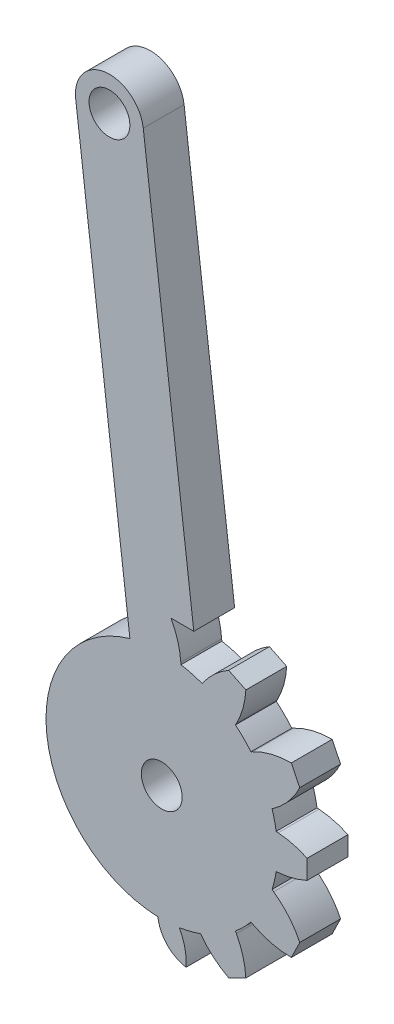
SolidWorks part; units mm, degrees
ref_plane "Front Plane" through (0, 0, 0) normal (0, 0, 1) x (1, 0, 0)
ref_plane "Top Plane" through (0, 0, 0) normal (0, 1, 0) x (1, 0, 0)
ref_plane "Right Plane" through (0, 0, 0) normal (1, 0, 0) x (0, 0, -1)
ref_plane "Plane1" through (0, 0, 1.9) normal (0, 0, 1) x (1, 0, 0)
sketch "Sketch1" plane through (0, 0, 1.9) normal (0, 0, 1) x (1, 0, 0)
  line L0 (-6.3198, 40.5143) -> (-2.3366, 8.1725)
  line L2 (0, 0) -> (-0.5241, -8.4838) construction
  line L3 (4.9124, -9.7818) -> (6.1789, -9.162)
  line L4 (5.4841, -6.684) -> (5.4141, -6.5527)
  line L5 (6.5527, -5.4141) -> (6.684, -5.4841)
  line L6 (9.5182, -6.1887) -> (10.138, -4.9222)
  line L7 (8.224, -2.6542) -> (8.1029, -2.5677)
  line L8 (8.4039, -1.2742) -> (8.5524, -1.2634)
  line L9 (10.6789, -0.705) -> (10.6789, 0.705)
  line L10 (8.5524, 1.2634) -> (8.4039, 1.2742)
  line L11 (8.1029, 2.5677) -> (8.224, 2.6542)
  line L12 (10.138, 4.9222) -> (9.5182, 6.1887)
  line L13 (6.684, 5.4841) -> (6.5527, 5.4141)
  line L14 (5.4141, 6.5527) -> (5.4841, 6.684)
  line L15 (6.1789, 9.162) -> (4.9124, 9.7818)
  line L16 (3.0542, 8.0862) -> (2.9677, 7.9651)
  line L17 (1.4124, 8.3818) -> (1.4016, 8.5302)
  line L18 (0.6785, 10.98) -> (2.3554, 10.98)
  line L19 (2.3554, 10.98) -> (-1.3573, 41.1255)
  line L20 (3.9551, -7.5277) -> (3.5177, -7.7418) construction
  line L21 (3.7364, -7.6347) -> (0, 0) construction
  circle A0 centre (-3.8386, 40.8199) radius 1.5
  arc A1 (-0.2838, -8.4953) -> (1.7876, -10.6761) centre (2.2, -8.2104) ccw
  arc A2 (6.1789, -9.162) -> (5.4841, -6.684) centre (0.1887, -9.5051) ccw
  arc A3 (5.4141, -6.5527) -> (6.5527, -5.4141) centre (0, 0) ccw
  arc A4 (6.684, -5.4841) -> (9.5182, -6.1887) centre (9.5051, -0.1887) ccw
  arc A5 (10.138, -4.9222) -> (8.224, -2.6542) centre (4.7381, -7.5377) ccw
  arc A6 (8.1029, -2.5677) -> (8.4039, -1.2742) centre (0, 0) ccw
  arc A7 (8.5524, -1.2634) -> (10.6789, -0.705) centre (8.1175, 4.7208) ccw
  arc A8 (10.6789, 0.705) -> (8.5524, 1.2634) centre (8.1175, -4.7208) ccw
  arc A9 (8.4039, 1.2742) -> (8.1029, 2.5677) centre (0, 0) ccw
  arc A10 (8.224, 2.6542) -> (10.138, 4.9222) centre (4.7381, 7.5377) ccw
  arc A11 (9.5182, 6.1887) -> (6.684, 5.4841) centre (9.5051, 0.1887) ccw
  arc A12 (6.5527, 5.4141) -> (5.4141, 6.5527) centre (0, 0) ccw
  arc A13 (5.4841, 6.684) -> (6.1789, 9.162) centre (0.1887, 9.5051) ccw
  arc A14 (4.9124, 9.7818) -> (3.0542, 8.0862) centre (7.9377, 4.6003) ccw
  arc A15 (2.9677, 7.9651) -> (1.4124, 8.3818) centre (0, 0) ccw
  arc A16 (1.4016, 8.5302) -> (0.6785, 10.98) centre (-4.5826, 8.0954) ccw
  arc A17 (-1.3573, 41.1255) -> (-6.3198, 40.5143) centre (-3.8386, 40.8199) ccw
  circle A18 centre (0, 0) radius 1.5
  circle A19 centre (0, 0) radius 8.5 construction
  arc A20 (2.8505, -8.0078) -> (4.9124, -9.7818) centre (7.6929, -4.465) ccw
  arc A21 (1.2894, -8.4016) -> (2.8505, -8.0078) centre (0, 0) ccw
  arc A22 (1.2894, -8.4016) -> (1.7876, -10.6761) centre (-2.2386, -10.3661) cw
  arc A23 (-0.2838, -8.4953) -> (-2.3366, 8.1725) centre (0, 0) cw
  point P61 (0, 0)
  point P62 (0, 0)
  point P64 (-0.2838, -8.4016)
  point P65 (0, 0)
  point P66 (0, 0)
  point P67 (0, 0)
  point P69 (0, 0)
  point P70 (0, 0)
  point P71 (0, 0)
  dimension "D1" = 3
  dimension "D2" = 2.5
  dimension "D3" = 1.61
  dimension "D4" = 8.5
  dimension "D5" = 6
  dimension "D6" = 0.6785
  dimension "D7" = 1.4016
  dimension "D8" = 1.4124
  dimension "D9" = 2.2
  dimension "D11" = 2.9677
  dimension "D12" = 3.0542
  dimension "D13" = 4.7381
  dimension "D14" = 4.9124
  dimension "D15" = 2.72
  dimension "D16" = 5.4141
  dimension "D17" = 6.5527
  dimension "D18" = 8.1175
  dimension "D19" = 41
  dimension "D20" = 2.7191
  dimension "D23" = 1.41
extrude "Boss-Extrude1" add sketch "Sketch1" against normal blind 3
